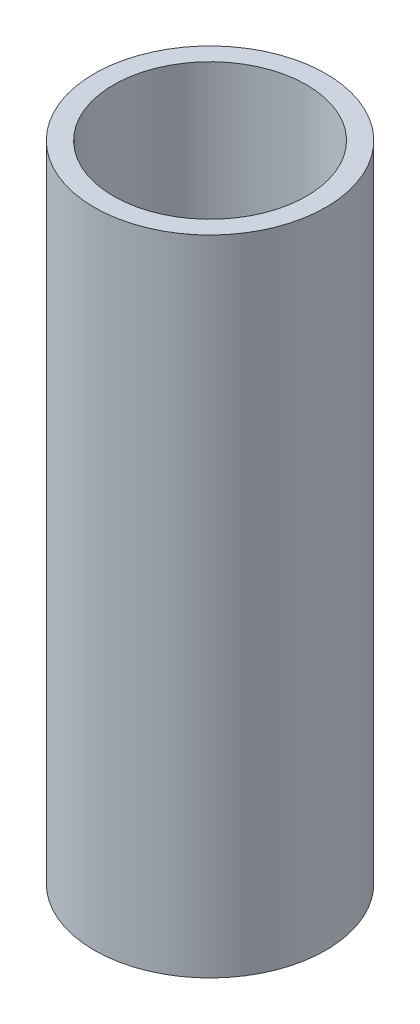
SolidWorks part; units mm, degrees
ref_plane "Front Plane" through (0, 0, 0) normal (0, 0, 1) x (1, 0, 0)
ref_plane "Top Plane" through (0, 0, 0) normal (0, 1, 0) x (1, 0, 0)
ref_plane "Right Plane" through (0, 0, 0) normal (1, 0, 0) x (0, 0, -1)
sketch "Sketch1" plane through (0, 0, 0) normal (0, 1, 0) x (1, 0, 0)
  circle A0 centre (0, 0) radius 18
  circle A1 centre (0, 0) radius 15
  dimension "D1" = 36
  dimension "D2" = 30
extrude "Boss-Extrude1" add sketch "Sketch1" along normal blind 100
